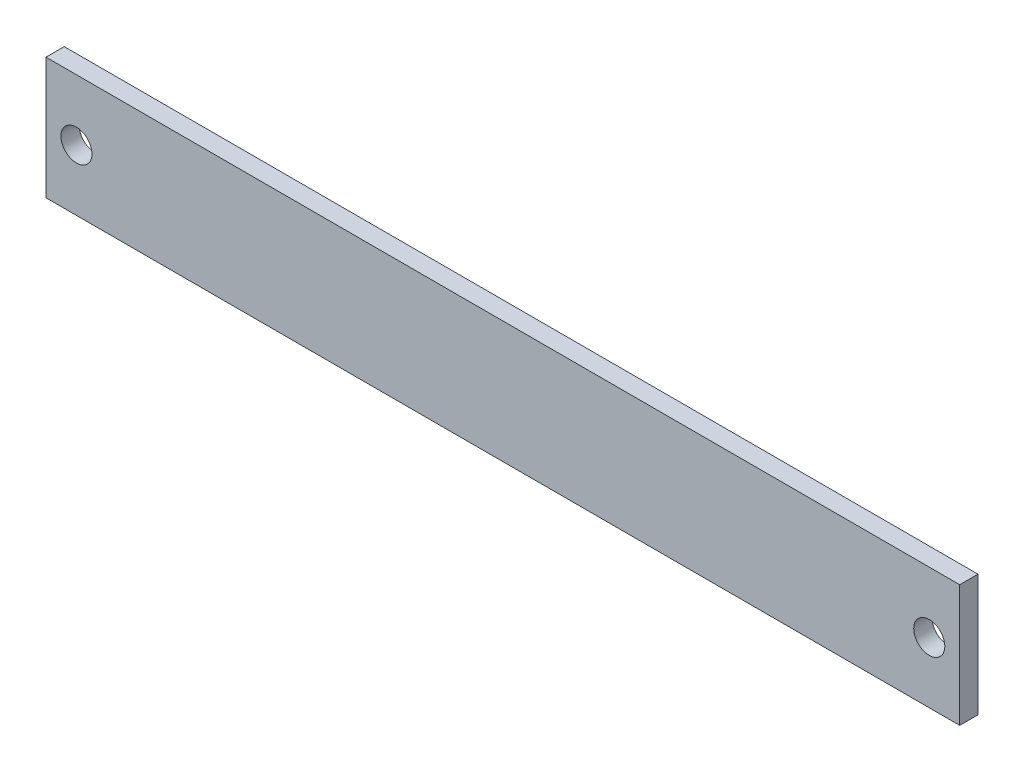
SolidWorks part; units mm, degrees
material "1023 Листовая углеродистая сталь (SS)"
ref_plane "Front" through (0, 0, 0) normal (0, 0, 1) x (1, 0, 0)
ref_plane "Top" through (0, 0, 0) normal (0, 1, 0) x (1, 0, 0)
ref_plane "Right" through (0, 0, 0) normal (1, 0, 0) x (0, 0, -1)
sketch "Sketch1" plane through (0, 0, 0) normal (0, 0, 1) x (1, 0, 0)
  line L0 (0, 0) -> (0, 45.8997) construction
  line L1 (-150, 20) -> (150, 20)
  line L2 (-150, 20) -> (-150, -20)
  line L3 (-150, -20) -> (150, -20)
  line L4 (150, 20) -> (150, -20)
  line L5 (-150, 20) -> (150, -20) construction
  line L6 (-150, -20) -> (150, 20) construction
  circle A0 centre (-140, 0) radius 5.1
  circle A1 centre (140, 0) radius 5.1
  point P0 (0, 0)
  dimension "D3" = 10.2
  dimension "D1" = 40
  dimension "D2" = 300
  dimension "D4" = 140
extrude "Extrude1" add sketch "Sketch1" along normal blind 6
